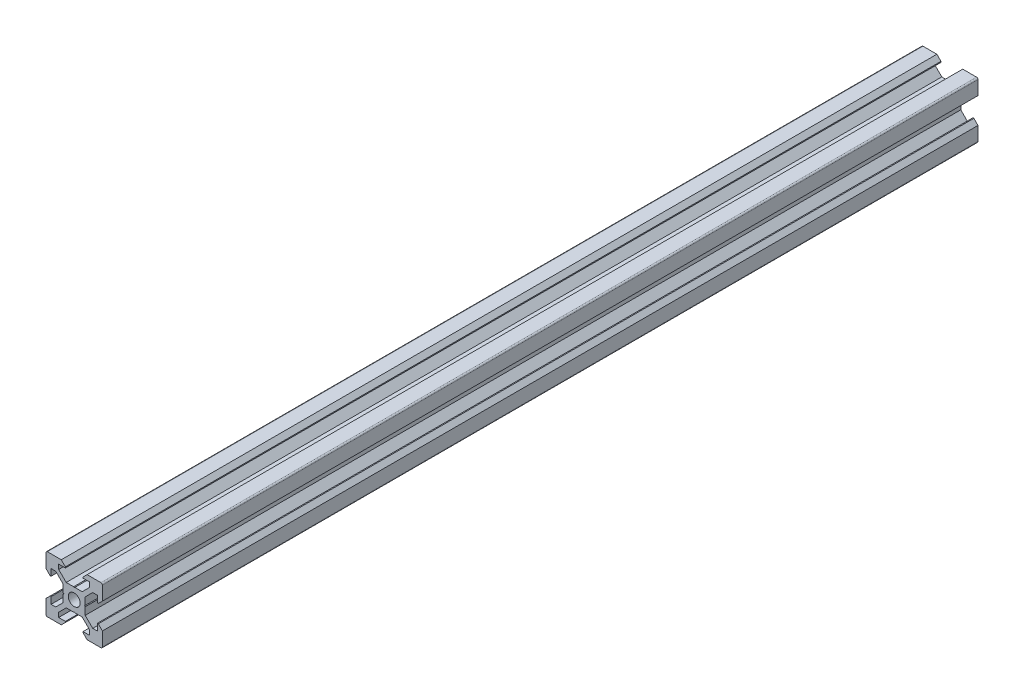
SolidWorks part; units mm, degrees
material "6061-T6 (SS)"
ref_plane "Front Plane" through (0, 0, 0) normal (0, 0, 1) x (1, 0, 0)
ref_plane "Top Plane" through (0, 0, 0) normal (0, 1, 0) x (1, 0, 0)
ref_plane "Right Plane" through (0, 0, 0) normal (1, 0, 0) x (0, 0, -1)
sketch "Sketch1" plane through (0, 0, 0) normal (0, 0, 1) x (1, 0, 0)
  line L1 (9.5, -10) -> (-9.5, -10)
  line L2 (10, -9.5) -> (10, 9.5)
  line L3 (9.5, 10) -> (-9.5, 10)
  line L4 (-10, -9.5) -> (-10, 9.5)
  line L5 (10, -10) -> (-10, 10) construction
  line L6 (10, 10) -> (-10, -10) construction
  circle A0 centre (0, 0) radius 2.1
  arc A1 (-9.5, 10) -> (-10, 9.5) centre (-9.5, 9.5) ccw
  arc A2 (10, 9.5) -> (9.5, 10) centre (9.5, 9.5) ccw
  arc A3 (9.5, -10) -> (10, -9.5) centre (9.5, -9.5) ccw
  arc A4 (-9.5, -10) -> (-10, -9.5) centre (-9.5, -9.5) cw
  point P0 (0, 0)
  line B0 (0, 0) -> (0, 10) construction
  line B1 (0, 3.69) -> (-0.21, 3.9)
  line B2 (-0.21, 3.9) -> (-2.8393, 3.9)
  line B3 (-2.8393, 3.9) -> (-5.5, 6.5607)
  line B4 (-5.5, 6.5607) -> (-5.5, 8.2)
  line B5 (-5.5, 8.2) -> (-3.125, 8.2)
  line B6 (-3.125, 8.2) -> (-3.125, 8.545)
  line B7 (-3.125, 8.545) -> (-4.58, 10)
  line B8 (-4.58, 10) -> (4.58, 10)
  line B9 (0, 0) -> (-5.9132, 5.9132) construction
  line B10 (3.125, 8.545) -> (4.58, 10)
  line B11 (3.125, 8.2) -> (3.125, 8.545)
  line B12 (5.5, 8.2) -> (3.125, 8.2)
  line B13 (5.5, 6.5607) -> (5.5, 8.2)
  line B14 (2.8393, 3.9) -> (5.5, 6.5607)
  line B15 (0.21, 3.9) -> (2.8393, 3.9)
  line B16 (0, 3.69) -> (0.21, 3.9)
  line B17 (0, 0) -> (-10, 0) construction
  line B18 (-3.69, 0) -> (-3.9, -0.21)
  line B19 (-3.9, -0.21) -> (-3.9, -2.8393)
  line B20 (-3.9, -2.8393) -> (-6.5607, -5.5)
  line B21 (-6.5607, -5.5) -> (-8.2, -5.5)
  line B22 (-8.2, -5.5) -> (-8.2, -3.125)
  line B23 (-8.2, -3.125) -> (-8.545, -3.125)
  line B24 (-8.545, -3.125) -> (-10, -4.58)
  line B25 (-10, -4.58) -> (-10, 4.58)
  line B26 (0, 0) -> (-5.9132, -5.9132) construction
  line B27 (-8.545, 3.125) -> (-10, 4.58)
  line B28 (-8.2, 3.125) -> (-8.545, 3.125)
  line B29 (-8.2, 5.5) -> (-8.2, 3.125)
  line B30 (-6.5607, 5.5) -> (-8.2, 5.5)
  line B31 (-3.9, 2.8393) -> (-6.5607, 5.5)
  line B32 (-3.9, 0.21) -> (-3.9, 2.8393)
  line B33 (-3.69, 0) -> (-3.9, 0.21)
  line B34 (0, 0) -> (0, -10) construction
  line B35 (0, -3.69) -> (0.21, -3.9)
  line B36 (0.21, -3.9) -> (2.8393, -3.9)
  line B37 (2.8393, -3.9) -> (5.5, -6.5607)
  line B38 (5.5, -6.5607) -> (5.5, -8.2)
  line B39 (5.5, -8.2) -> (3.125, -8.2)
  line B40 (3.125, -8.2) -> (3.125, -8.545)
  line B41 (3.125, -8.545) -> (4.58, -10)
  line B42 (4.58, -10) -> (-4.58, -10)
  line B43 (0, 0) -> (5.9132, -5.9132) construction
  line B44 (-3.125, -8.545) -> (-4.58, -10)
  line B45 (-3.125, -8.2) -> (-3.125, -8.545)
  line B46 (-5.5, -8.2) -> (-3.125, -8.2)
  line B47 (-5.5, -6.5607) -> (-5.5, -8.2)
  line B48 (-2.8393, -3.9) -> (-5.5, -6.5607)
  line B49 (-0.21, -3.9) -> (-2.8393, -3.9)
  line B50 (0, -3.69) -> (-0.21, -3.9)
  line B51 (0, 0) -> (10, 0) construction
  line B52 (3.69, 0) -> (3.9, 0.21)
  line B53 (3.9, 0.21) -> (3.9, 2.8393)
  line B54 (3.9, 2.8393) -> (6.5607, 5.5)
  line B55 (6.5607, 5.5) -> (8.2, 5.5)
  line B56 (8.2, 5.5) -> (8.2, 3.125)
  line B57 (8.2, 3.125) -> (8.545, 3.125)
  line B58 (8.545, 3.125) -> (10, 4.58)
  line B59 (10, 4.58) -> (10, -4.58)
  line B60 (0, 0) -> (5.9132, 5.9132) construction
  line B61 (8.545, -3.125) -> (10, -4.58)
  line B62 (8.2, -3.125) -> (8.545, -3.125)
  line B63 (8.2, -5.5) -> (8.2, -3.125)
  line B64 (6.5607, -5.5) -> (8.2, -5.5)
  line B65 (3.9, -2.8393) -> (6.5607, -5.5)
  line B66 (3.9, -0.21) -> (3.9, -2.8393)
  line B67 (3.69, 0) -> (3.9, -0.21)
  dimension "D1" = 4.2
  dimension "D3" = 0.5
  dimension "D2" = 20
sketch_block_instance "V Slot 1-4"
sketch_block "V Slot 1" parameters "D1"=10, "D2"=11, "D3"=4.3, "D4"=1.8, "D5"=0.21, "D6"=45, "D7"=9.16, "D8"=1.5, "D9"=6.25
sketch_block_instance "V Slot 1-5"
sketch_block_instance "V Slot 1-6"
sketch_block_instance "V Slot 1-7"
extrude "Boss-Extrude1" add sketch "Sketch1" along normal blind 310.45 contours B67 B52 B53 B54 B55 B56 B57 B58 L2 A2 L3 B10 B11 B12 B13 B14 B15 B16 B1 B2 B3 B4 B5 B6 B7 A1 L4 B27 B28 B29 B30 B31 B32 B33 B18 B19 B20 B21 B22 B23 B24 A4 L1 B44 B45 B46 B47 B48 B49
